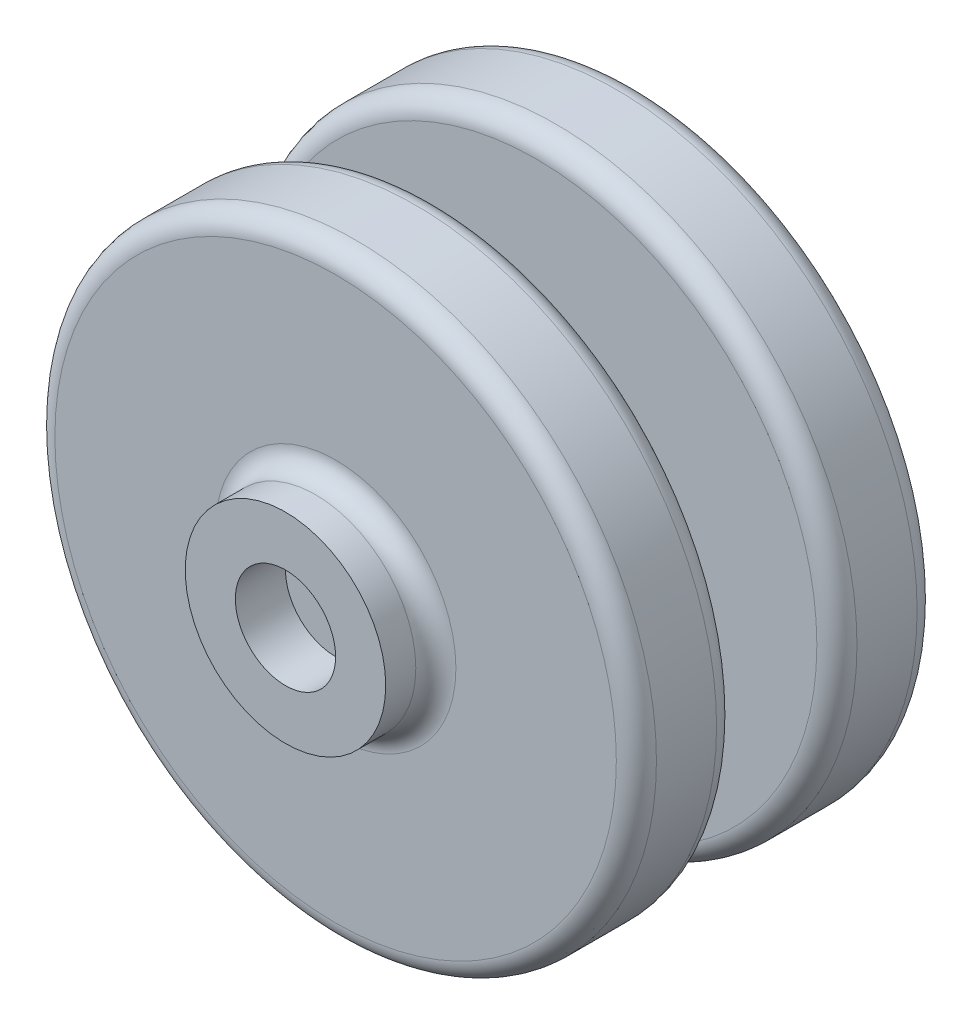
SolidWorks part; units mm, degrees
material "Plain Carbon Steel"
ref_plane "Front Plane" through (0, 0, 0) normal (0, 0, 1) x (1, 0, 0)
ref_plane "Top Plane" through (0, 0, 0) normal (0, 1, 0) x (1, 0, 0)
ref_plane "Right Plane" through (0, 0, 0) normal (1, 0, 0) x (0, 0, -1)
sketch "Sketch1" plane through (0, 0, 0) normal (0, 0, 1) x (1, 0, 0)
  circle A0 centre (0, 0) radius 30
  dimension "D1" = 60
extrude "Boss-Extrude1" add sketch "Sketch1" along normal blind 10
sketch "Sketch2" plane through (0, 0, 10) normal (0, 0, 1) x (1, 0, 0)
  circle A0 centre (0, 0) radius 5
  dimension "D1" = 10
extrude "Boss-Extrude2" add sketch "Sketch2" along normal blind 10
sketch "Sketch3" plane through (0, 0, 20) normal (0, 0, 1) x (1, 0, 0)
  circle A0 centre (0, 0) radius 30
  dimension "D1" = 60
extrude "Boss-Extrude3" add sketch "Sketch3" along normal blind 10
sketch "Sketch5" plane through (0, 0, 30) normal (0, 0, 1) x (1, 0, 0)
  circle A0 centre (0, 0) radius 5
  circle A1 centre (0, 0) radius 10
  dimension "D1" = 10
  dimension "D2" = 20
extrude "Boss-Extrude5" add sketch "Sketch5" along normal blind 5
ref_plane "Plane1" through (0, 0, 15) normal (0, 0, 1) x (1, 0, 0)
mirror "Mirror1" about plane through (0, 0, 15) normal (0, 0, 1) of "Boss-Extrude5"
fillet "Fillet1" radius 2 2 edges at (10, 0, 0) (10, 0, 30)
fillet "Fillet2" radius 2 4 edges at (30, 0, 30) (30, 0, 20) (30, 0, 10) (30, 0, 0)
